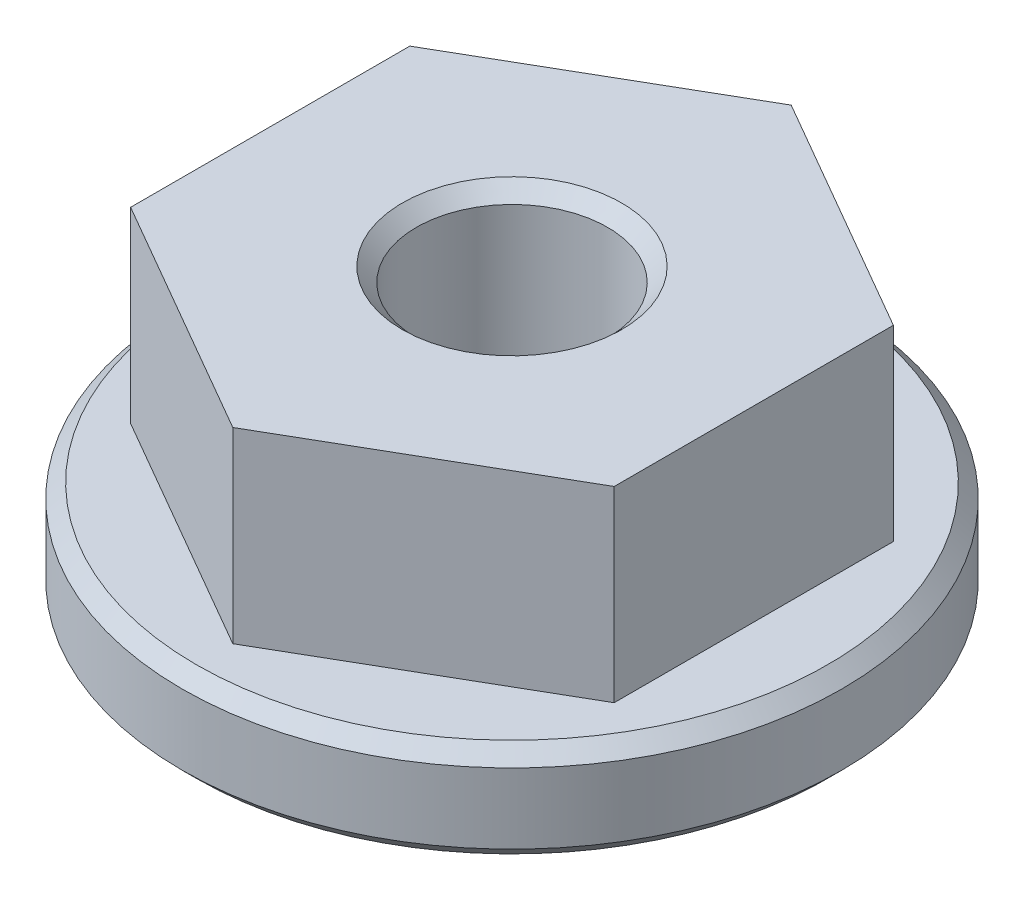
SolidWorks part; units mm, degrees
ref_plane "Front Plane" through (0, 0, 0) normal (0, 0, 1) x (1, 0, 0)
ref_plane "Top Plane" through (0, 0, 0) normal (0, 1, 0) x (1, 0, 0)
ref_plane "Right Plane" through (0, 0, 0) normal (1, 0, 0) x (0, 0, -1)
sketch "Sketch1" plane through (0, 0, 0) normal (0, 1, 0) x (1, 0, 0)
  circle A0 centre (0, 0) radius 5.9531
  dimension "D1" = 11.9062
extrude "Boss-Extrude1" add sketch "Sketch1" along normal blind 1.778
sketch "Sketch2" plane through (0, 1.778, 0) normal (0, 1, 0) x (1, 0, 0)
  line L1 (4.3656, -2.5205) -> (4.3656, 2.5205)
  line L2 (4.3656, 2.5205) -> (0, 5.041)
  line L3 (0, 5.041) -> (-4.3656, 2.5205)
  line L4 (-4.3656, 2.5205) -> (-4.3656, -2.5205)
  line L5 (-4.3656, -2.5205) -> (0, -5.041)
  line L6 (0, -5.041) -> (4.3656, -2.5205)
  circle A0 centre (0, 0) radius 4.3656 construction
  circle A1 centre (0, 0) radius 5.9531 construction
  point P11 (0, 0)
  dimension "D1" = 8.7312
extrude "Boss-Extrude2" add sketch "Sketch2" along normal blind 3.3814
hole_wizard "#8-32 Tapped Hole1" positions "Sketch3" profile "Sketch4" tap size "#8-32" standard "ANSI Inch" end condition through all
sketch "Sketch3" plane through (0, 5.1594, 0) normal (0, 1, 0) x (1, 0, 0)
  point P0 (0, 0)
sketch "Sketch4" plane through (0, 5.1594, 0) normal (1, 0, 0) x (0, 0, 1)
  line L0 (0, 0) -> (0, 5.1594)
  line L1 (0, 5.1594) -> (1.7272, 5.1594)
  line L2 (1.7272, 5.1594) -> (1.7272, 0)
  line L5 (1.7272, 0) -> (0, 0)
  line L11 (0, -6.35) -> (0, 107.95) construction
  dimension "Thru Tap Drill Dia." = 3.4544
  dimension "Thru Tap Drill Depth" = 5.1594
cosmetic thread "Hole Thread1" parameters "D2"=4.1656
chamfer "Chamfer1" distance 0.254 angle 45 4 edges at (0, 0, 1.7272) (0, 5.1594, 1.7272) (0, 1.778, 5.9531) (0, 0, 5.9531)
